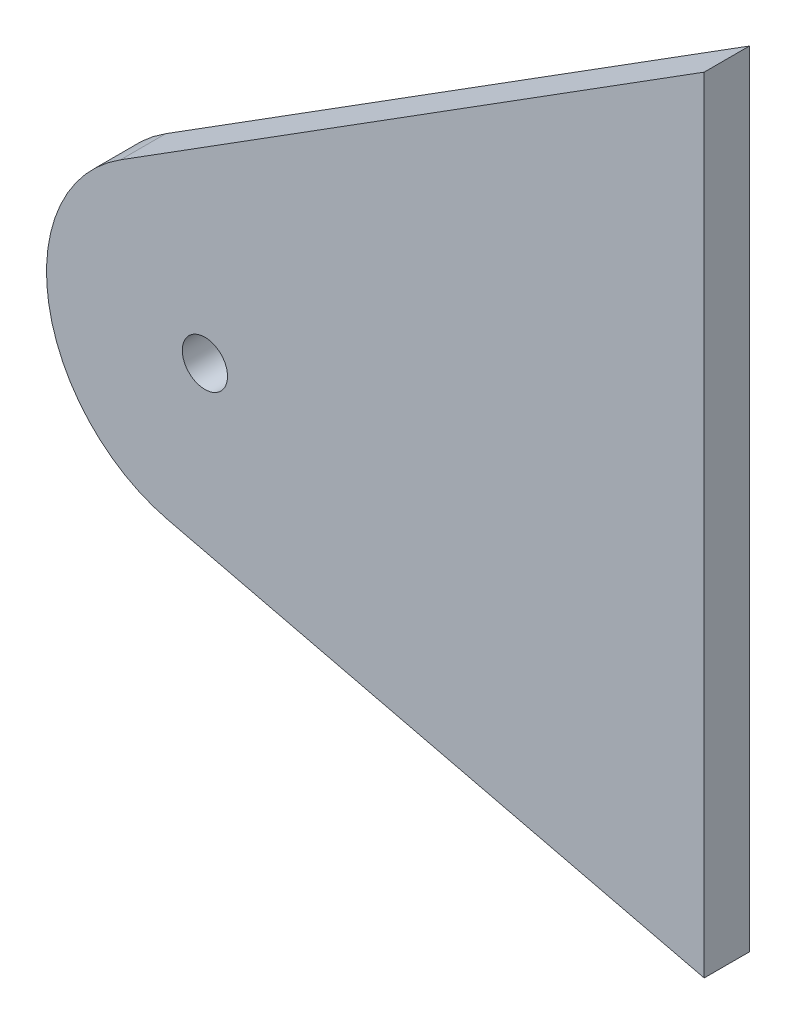
SolidWorks part; units mm, degrees
material "Resina de poliéster"
ref_plane "Alzado" through (0, 0, 0) normal (0, 0, 1) x (1, 0, 0)
ref_plane "Planta" through (0, 0, 0) normal (0, 1, 0) x (1, 0, 0)
ref_plane "Vista lateral" through (0, 0, 0) normal (1, 0, 0) x (0, 0, -1)
sketch "Model" plane through (0, 0, 0) normal (0, 0, 1) x (1, 0, 0)
  line L71 (33.0926, 33.2617) -> (33.0926, 20.3647)
  line L72 (0, 1.4) -> (0, -1.4) construction
  line L75 (33.0926, 33.2617) -> (33.0926, -18.7383)
  line L76 (33.0926, 33.2617) -> (-5.5974, 8.8836)
  line L77 (33.0926, -18.7383) -> (-2.4499, -10.2102)
  line L84 (1.4, 0) -> (-1.5, 0) construction
  arc A108 (-5.5974, 8.8836) -> (-2.4499, -10.2102) centre (0, 0) ccw
  circle A109 centre (0, 0) radius 1.5
  point P374 (-1.5, 0)
  point P375 (1.5, 0)
  dimension "D6" = 1.5
  dimension "D3" = 18.7383
  dimension "D4" = 52
  dimension "D5" = 3
  dimension "D7" = 33.0926
extrude "Saliente-Extruir1" add sketch "Model" along normal blind 3 contours L76 A108 L77 L75 L71 A109
